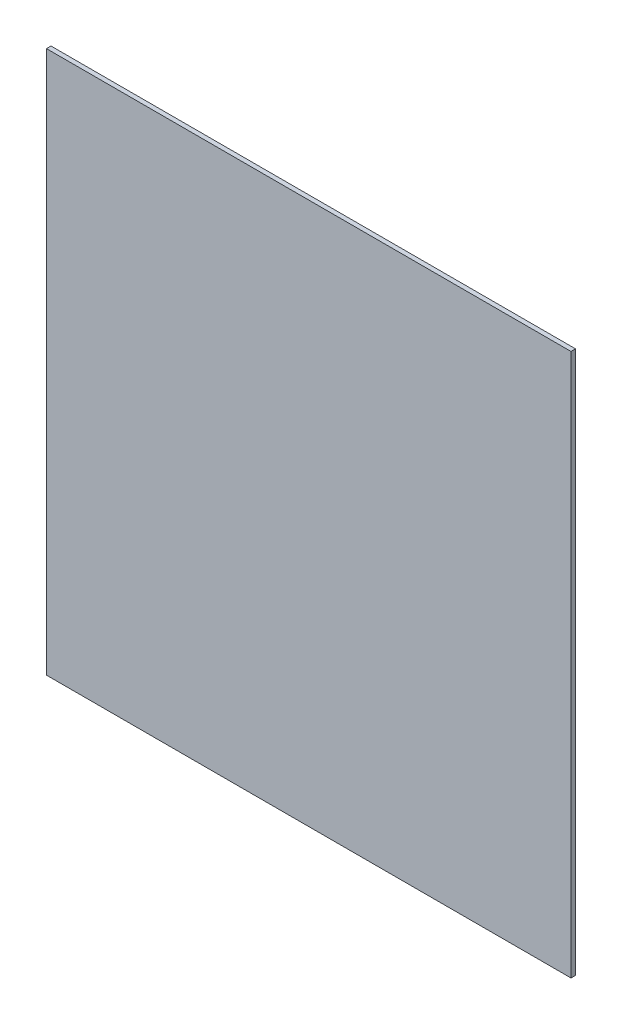
SolidWorks part; units mm, degrees
ref_plane "Front Plane" through (0, 0, 0) normal (0, 0, 1) x (1, 0, 0)
ref_plane "Top Plane" through (0, 0, 0) normal (0, 1, 0) x (1, 0, 0)
ref_plane "Right Plane" through (0, 0, 0) normal (1, 0, 0) x (0, 0, -1)
sketch "Sketch1" plane through (0, 0, 0) normal (0, 0, 1) x (1, 0, 0)
  line L1 (-290, 300) -> (290, 300)
  line L2 (-290, 300) -> (-290, -300)
  line L3 (-290, -300) -> (290, -300)
  line L4 (290, 300) -> (290, -300)
  line L5 (-290, 300) -> (290, -300) construction
  line L6 (-290, -300) -> (290, 300) construction
  point P0 (0, 0)
  dimension "D1" = 600
  dimension "D2" = 580
extrude "Boss-Extrude1" add sketch "Sketch1" along normal blind 5
